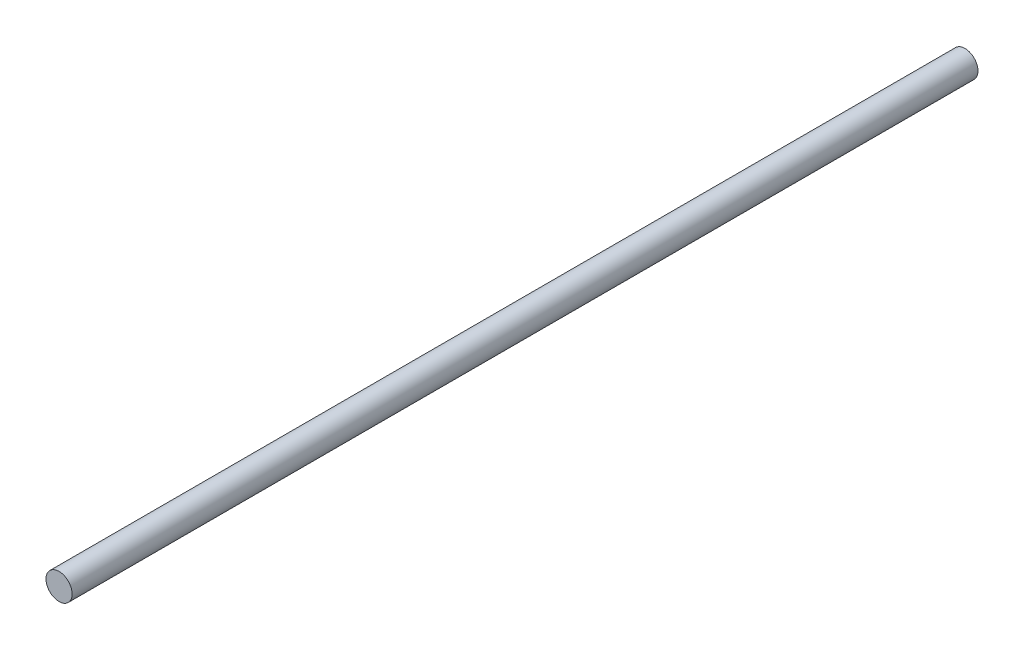
SolidWorks part; units mm, degrees
material "Plain Carbon Steel"
ref_plane "Front Plane" through (0, 0, 0) normal (0, 0, 1) x (1, 0, 0)
ref_plane "Top Plane" through (0, 0, 0) normal (0, 1, 0) x (1, 0, 0)
ref_plane "Right Plane" through (0, 0, 0) normal (1, 0, 0) x (0, 0, -1)
sketch "Sketch1" plane through (0, 0, 0) normal (0, 0, 1) x (1, 0, 0)
  circle A0 centre (0, 0) radius 1.5
extrude "Boss-Extrude1" add sketch "Sketch1" along normal blind 104
